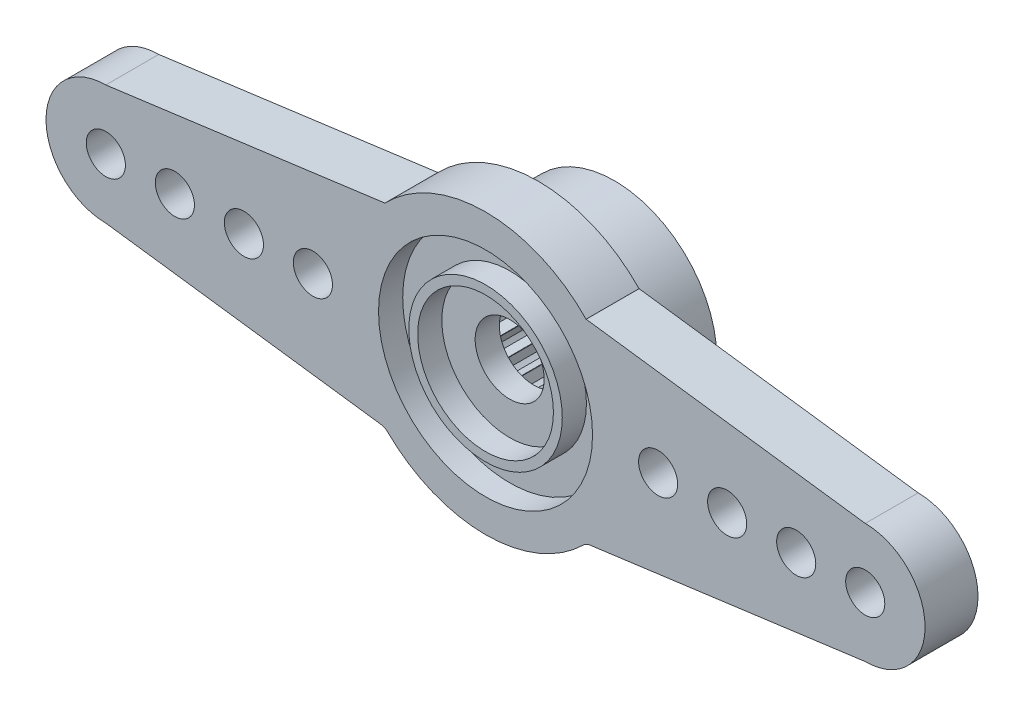
SolidWorks part; units mm, degrees
ref_plane "Ön Düzlem" through (0, 0, 0) normal (0, 0, 1) x (1, 0, 0)
ref_plane "Üst Düzlem" through (0, 0, 0) normal (0, 1, 0) x (1, 0, 0)
ref_plane "Sağ Düzlem" through (0, 0, 0) normal (1, 0, 0) x (0, 0, -1)
sketch "Çizim1" plane through (0, 0, 0) normal (0, 0, 1) x (1, 0, 0)
  circle A0 centre (0, 0) radius 4.45
  dimension "D1" = 8.9
extrude "Yükseklik-Ekstrüzyon1" add sketch "Çizim1" along normal blind 5.6
sketch "Çizim2" plane through (0, 0, 5.6) normal (0, 0, 1) x (1, 0, 0)
  line L0 (-4.3703, 4.22) -> (-4.37, 4.22)
  line L1 (4.37, 4.22) -> (4.3703, 4.22)
  line L2 (16.5, 2.6) -> (4.357, 4.2218)
  line L3 (16.5, -2.6) -> (4.357, -4.2218)
  line L4 (0, 0) -> (0, -5.2717) construction
  line L5 (-16.5, 2.6) -> (-4.357, 4.2218)
  line L6 (-16.5, -2.6) -> (-4.357, -4.2218)
  arc A1 (-4.37, -4.22) -> (4.37, -4.22) centre (0, 0) ccw
  arc A2 (16.5, -2.6) -> (16.5, 2.6) centre (16.5, 0) ccw
  circle A4 centre (7.5, 0) radius 0.85
  circle A5 centre (10.5, 0) radius 0.85
  circle A6 centre (13.5, 0) radius 0.85
  circle A7 centre (16.5, 0) radius 0.85
  circle A8 centre (-16.5, 0) radius 0.85
  circle A9 centre (-13.5, 0) radius 0.85
  circle A10 centre (-10.5, 0) radius 0.85
  circle A11 centre (-7.5, 0) radius 0.85
  arc A12 (4.37, 4.22) -> (-4.37, 4.22) centre (0, 0) ccw
  arc A13 (-16.5, -2.6) -> (-16.5, 2.6) centre (-16.5, 0) cw
  dimension "D1" = 4.22
  dimension "D2" = 1.7
  dimension "D3" = 1.7
  dimension "D4" = 3
  dimension "D5" = 3
  dimension "D6" = 3
extrude "Yükseklik-Ekstrüzyon3" add sketch "Çizim2" against normal blind 2.3
fillet "Radyus1" radius 0.5 4 edges at (-4.37, -4.22, 4.45) (4.37, -4.22, 4.45) (-4.3703, 4.22, 4.45) (4.3703, 4.22, 4.45)
sketch "Çizim3" plane through (0, 0, 0) normal (0, 0, -1) x (-1, 0, 0)
  circle A0 centre (0, 0) radius 2.95
  dimension "D1" = 5.9
extrude "Kes-Ekstrüzyon1" cut sketch "Çizim3" against normal blind 1.05
sketch "Çizim7" plane through (0, 0, 5.6) normal (0, 0, 1) x (1, 0, 0)
  circle A0 centre (0, 0) radius 2.95
  circle A1 centre (0, 0) radius 3.335
  circle A2 centre (0, 0) radius 4.65
  dimension "D1" = 5.9
  dimension "D2" = 6.67
  dimension "D3" = 9.3
extrude "Kes-Ekstrüzyon3" cut sketch "Çizim7" against normal blind 1.05 contours A2 A1
sketch "Çizim8" plane through (0, 0, 5.6) normal (0, 0, 1) x (1, 0, 0)
  circle A0 centre (0, 0) radius 2.95
  dimension "D1" = 5.9
extrude "Kes-Ekstrüzyon5" cut sketch "Çizim8" against normal blind 1.05
sketch "Çizim9" plane through (0, 0, 1.05) normal (0, 0, -1) x (-1, 0, 0)
  circle A0 centre (0, 0) radius 2.95
extrude "Yükseklik-Ekstrüzyon4" add sketch "Çizim9" along normal blind 1.05
sketch "Çizim10" plane through (0, 0, 4.55) normal (0, 0, 1) x (1, 0, 0)
  circle A0 centre (0, 0) radius 1.5
extrude "Kes-Ekstrüzyon6" cut sketch "Çizim10" against normal blind 8.05
sketch "Çizim11" plane through (0, 0, 0) normal (0, 0, -1) x (-1, 0, 0)
  circle A1 centre (0, 0) radius 2.68
extrude "Kes-Ekstrüzyon7" cut sketch "Çizim11" against normal blind 3.5
sketch "Çizim12" plane through (0, 0, 3.5) normal (0, 0, -1) x (-1, 0, 0)
  line L13 (-2.0003, 2.3025) -> (-1.9385, 1.8506)
  line L14 (-1.8371, 2.4346) -> (-1.4079, 2.2804)
  arc A3 (-1.4079, 2.2804) -> (-1.9385, 1.8506) centre (0, 0) ccw
  arc A4 (-1.8371, 2.4346) -> (-2.0003, 2.3025) centre (0, 0) ccw
extrude "Kes-Ekstrüzyon10" cut sketch "Çizim12" along normal blind 12.5
pattern_circular "Dairesel Kaplama1" count 25 every 15 about axis through (0, 0, 0) along (0, 0, 1) of "Kes-Ekstrüzyon10"
